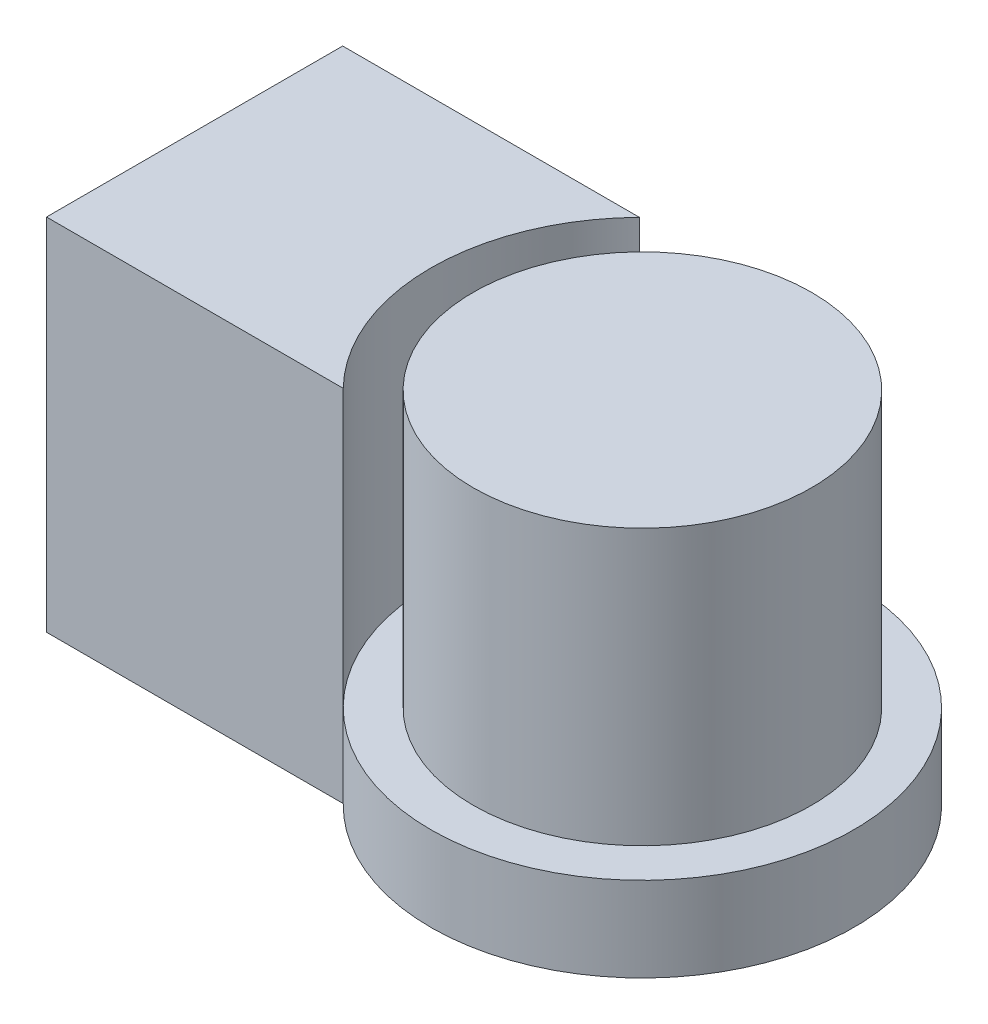
SolidWorks part; units mm, degrees
ref_plane "Front" through (0, 0, 0) normal (0, 0, 1) x (1, 0, 0)
ref_plane "Top" through (0, 0, 0) normal (0, 1, 0) x (1, 0, 0)
ref_plane "Right" through (0, 0, 0) normal (1, 0, 0) x (0, 0, -1)
sketch "Sketch1" plane through (0, 0, 0) normal (0, 1, 0) x (1, 0, 0)
  circle A0 centre (0, 0) radius 50
extrude "Extrude1" add sketch "Sketch1" along normal blind 20
sketch "Sketch2" plane through (0, 20, 0) normal (0, 1, 0) x (-1, 0, 0)
  circle A0 centre (0, 0) radius 40
extrude "Extrude2" add sketch "Sketch2" along normal blind 65 separate body
sketch "Sketch3" plane through (0, 0, 0) normal (0, 1, 0) x (1, 0, 0)
  line L1 (-105.8382, 35) -> (-105.8382, -35)
  line L4 (-105.8382, -35) -> (-35.7071, -35)
  line L5 (-105.8382, 35) -> (-35.7071, 35)
  arc A0 (-35.7071, 35) -> (-35.7071, -35) centre (0, 0) ccw
extrude "Extrude3" add sketch "Sketch3" along normal blind 85
